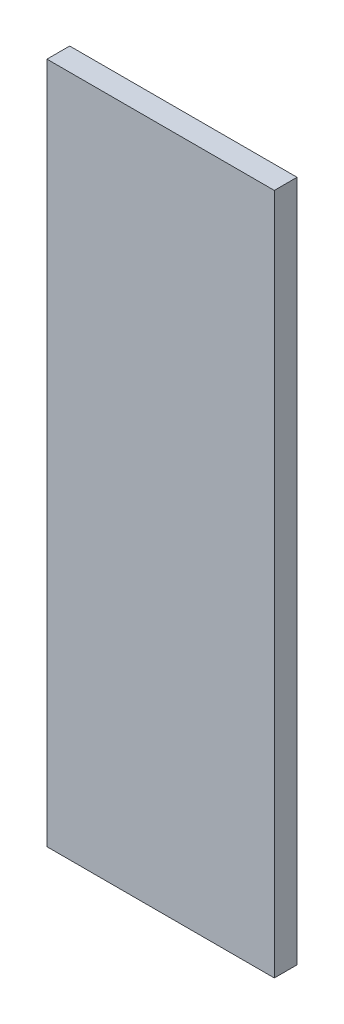
SolidWorks part; units mm, degrees
ref_plane "Piano frontale" through (0, 0, 0) normal (0, 0, 1) x (1, 0, 0)
ref_plane "Piano superiore" through (0, 0, 0) normal (0, 1, 0) x (1, 0, 0)
ref_plane "Piano destro" through (0, 0, 0) normal (1, 0, 0) x (0, 0, -1)
sketch "Schizzo1" plane through (0, 0, 0) normal (0, 0, 1) x (1, 0, 0)
  line L1 (-5, 15) -> (5, 15)
  line L2 (-5, 15) -> (-5, -15)
  line L3 (-5, -15) -> (5, -15)
  line L4 (5, 15) -> (5, -15)
  line L5 (-5, 15) -> (5, -15) construction
  line L6 (-5, -15) -> (5, 15) construction
  point P0 (0, 0)
  dimension "D1" = 10
  dimension "D2" = 30
extrude "Estrusione-Estrusione1" add sketch "Schizzo1" along normal blind 1
